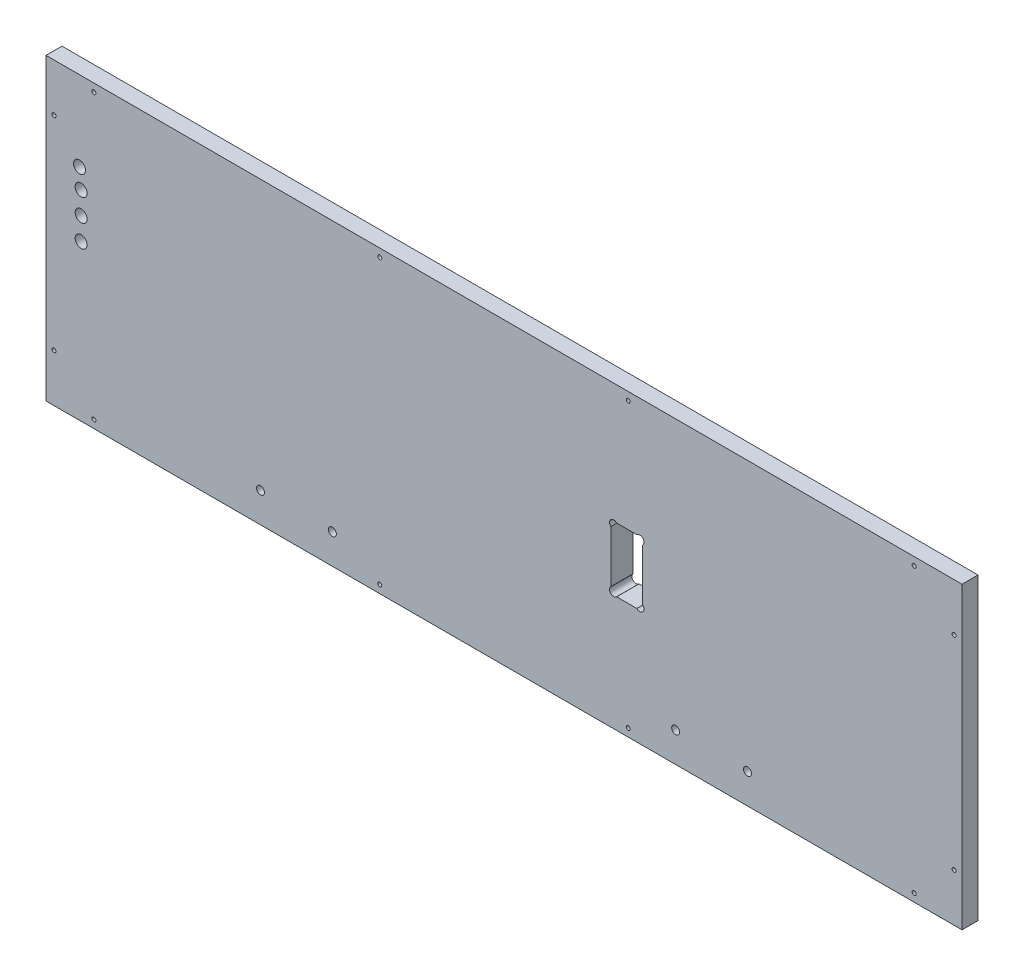
SolidWorks part; units mm, degrees
material "Pine"
ref_plane "Front Plane" through (0, 0, 0) normal (0, 0, 1) x (1, 0, 0)
ref_plane "Top Plane" through (0, 0, 0) normal (0, 1, 0) x (1, 0, 0)
ref_plane "Right Plane" through (0, 0, 0) normal (1, 0, 0) x (0, 0, -1)
sketch "Sketch1" plane through (0, 0, 0) normal (0, 0, 1) x (1, 0, 0)
  line L0 (-5300.6625, 1520.825) -> (-5451.475, 1520.825)
  line L1 (-5456.2375, 1384.3) -> (-5456.2375, 1516.0625)
  line L2 (-5557.8375, 1546.225) -> (-5194.3, 1546.225)
  line L3 (-5557.8375, 1539.875) -> (-5194.3, 1539.875)
  line L4 (-5297.4875, 1377.95) -> (-5454.65, 1377.95)
  line L5 (-5291.1375, 1384.3) -> (-5291.1375, 1516.0625)
  line L6 (-5300.6625, 1525.5875) -> (-5451.475, 1525.5875)
  line L7 (-5461, 1384.3) -> (-5461, 1516.0625)
  line L8 (-5297.4875, 1382.7125) -> (-5454.65, 1382.7125)
  line L9 (-5295.9, 1384.3) -> (-5295.9, 1516.0625)
  line L10 (-5740.4, 998.5375) -> (-5740.4, 1181.1)
  line L11 (-5740.4, 1181.1) -> (-5512.5938, 1181.1)
  line L12 (-5512.5938, 1181.1) -> (-5512.5938, 998.5375)
  line L13 (-5512.5938, 998.5375) -> (-5740.4, 998.5375)
  line L14 (-5258.5938, 1181.1) -> (-5486.4, 1181.1)
  line L15 (-5258.5938, 998.5375) -> (-5258.5938, 1181.1)
  line L16 (-5486.4, 998.5375) -> (-5258.5938, 998.5375)
  line L17 (-5486.4, 1181.1) -> (-5486.4, 998.5375)
  line L18 (-5740.4, 898.525) -> (-5011.7375, 898.525)
  line L19 (-5168.1062, 1384.3) -> (-5168.1062, 1392.2375)
  line L20 (-5176.0437, 1400.175) -> (-5245.8937, 1400.175)
  line L21 (-5253.8313, 1392.2375) -> (-5253.8313, 1384.3)
  line L22 (-5451.475, 1512.8875) -> (-5451.475, 1384.3)
  line L23 (-5303.8375, 1516.0625) -> (-5448.3, 1516.0625)
  line L24 (-5498.3062, 1384.3) -> (-5451.475, 1384.3)
  line L25 (-5253.8313, 1384.3) -> (-5300.6625, 1384.3)
  line L26 (-5584.0312, 1384.3) -> (-5740.4, 1384.3)
  line L27 (-5564.1875, 1536.7) -> (-5740.4, 1536.7)
  line L28 (-5740.4, 1357.3125) -> (-5740.4, 1206.5)
  line L29 (-5011.7375, 1357.3125) -> (-5740.4, 1357.3125)
  line L30 (-5011.7375, 1206.5) -> (-5011.7375, 1357.3125)
  line L31 (-5740.4, 1206.5) -> (-5011.7375, 1206.5)
  line L32 (-4765.675, 1549.4) -> (-4978.4, 1549.4)
  line L33 (-4765.675, 1397) -> (-4765.675, 1549.4)
  line L34 (-4978.4, 1397) -> (-4765.675, 1397)
  line L35 (-4978.4, 1549.4) -> (-4978.4, 1397)
  line L36 (-4765.675, 1371.6) -> (-4978.4, 1371.6)
  line L37 (-4765.675, 1219.2) -> (-4765.675, 1371.6)
  line L38 (-4978.4, 1219.2) -> (-4765.675, 1219.2)
  line L39 (-4978.4, 1371.6) -> (-4978.4, 1219.2)
  line L40 (-5284.7875, 803.275) -> (-5272.0875, 803.275)
  line L41 (-5187.95, 1536.7) -> (-5011.7375, 1536.7)
  line L42 (-5300.6625, 1384.3) -> (-5300.6625, 1512.8875)
  line L43 (-5740.4, 1536.7) -> (-5740.4, 1384.3)
  line L44 (-5557.8375, 1536.7) -> (-5557.8375, 1549.4)
  line L45 (-5557.8375, 1549.4) -> (-5194.3, 1549.4)
  line L46 (-5194.3, 1549.4) -> (-5194.3, 1536.7)
  line L47 (-5011.7375, 1536.7) -> (-5011.7375, 1384.3)
  line L48 (-5011.7375, 1384.3) -> (-5168.1062, 1384.3)
  line L49 (-5498.3062, 1384.3) -> (-5498.3062, 1392.2375)
  line L50 (-5506.2437, 1400.175) -> (-5576.0938, 1400.175)
  line L51 (-5584.0312, 1392.2375) -> (-5584.0312, 1384.3)
  line L52 (-5740.4, 660.4) -> (-5740.4, 898.525)
  line L53 (-5011.7375, 898.525) -> (-5011.7375, 660.4)
  line L54 (-5011.7375, 660.4) -> (-5740.4, 660.4)
  line L55 (-5291.1375, 803.275) -> (-5291.1375, 752.475)
  line L56 (-5265.7375, 752.475) -> (-5265.7375, 803.275)
  line L57 (-5284.7875, 752.475) -> (-5272.0875, 752.475)
  arc A0 (-5451.475, 1520.825) -> (-5456.2375, 1516.0625) centre (-5451.475, 1516.0625) ccw
  arc A1 (-5461, 1384.3) -> (-5454.65, 1377.95) centre (-5454.65, 1384.3) ccw
  arc A2 (-5297.4875, 1377.95) -> (-5291.1375, 1384.3) centre (-5297.4875, 1384.3) ccw
  circle A3 centre (-5037.9312, 1233.4875) radius 1.5875
  circle A4 centre (-5037.9312, 1328.7375) radius 1.5875
  circle A5 centre (-5714.2063, 1233.4875) radius 1.5875
  circle A6 centre (-5714.2063, 1328.7375) radius 1.5875
  circle A7 centre (-5018.0875, 1333.5) radius 1.5875
  circle A8 centre (-5018.0875, 1231.9) radius 1.5875
  circle A9 centre (-5734.05, 1231.9) radius 1.5875
  circle A10 centre (-5734.05, 1333.5) radius 1.5875
  circle A11 centre (-5734.05, 1511.3) radius 1.5875
  circle A12 centre (-5734.05, 1409.7) radius 1.5875
  circle A13 centre (-5018.0875, 1511.3) radius 1.5875
  circle A14 centre (-5018.0875, 1409.7) radius 1.5875
  arc A15 (-5557.8375, 1546.225) -> (-5557.8375, 1539.875) centre (-5557.8375, 1543.05) ccw
  arc A16 (-5194.3, 1539.875) -> (-5194.3, 1546.225) centre (-5194.3, 1543.05) ccw
  arc A17 (-5291.1375, 1516.0625) -> (-5300.6625, 1525.5875) centre (-5300.6625, 1516.0625) ccw
  arc A18 (-5451.475, 1525.5875) -> (-5461, 1516.0625) centre (-5451.475, 1516.0625) ccw
  arc A19 (-5456.2375, 1384.3) -> (-5454.65, 1382.7125) centre (-5454.65, 1384.3) ccw
  arc A20 (-5297.4875, 1382.7125) -> (-5295.9, 1384.3) centre (-5297.4875, 1384.3) ccw
  arc A21 (-5295.9, 1516.0625) -> (-5300.6625, 1520.825) centre (-5300.6625, 1516.0625) ccw
  circle A22 centre (-5702.3, 892.175) radius 1.5875
  circle A23 centre (-5734.05, 860.425) radius 1.5875
  circle A24 centre (-5474.8906, 892.175) radius 1.5875
  circle A25 centre (-5277.2469, 892.175) radius 1.5875
  circle A26 centre (-5049.8375, 892.175) radius 1.5875
  circle A27 centre (-5018.0875, 860.425) radius 1.5875
  circle A28 centre (-5296.6938, 1174.75) radius 1.5875
  circle A29 centre (-5448.3, 1174.75) radius 1.5875
  circle A30 centre (-5264.9437, 1155.7) radius 1.5875
  circle A31 centre (-5264.9437, 1023.9375) radius 1.5875
  circle A32 centre (-5518.9438, 1155.7) radius 1.5875
  circle A33 centre (-5518.9438, 1023.9375) radius 1.5875
  circle A34 centre (-5702.3, 1004.8875) radius 1.5875
  circle A35 centre (-5550.6937, 1004.8875) radius 1.5875
  arc A36 (-5576.0938, 1400.175) -> (-5584.0312, 1392.2375) centre (-5576.0938, 1392.2375) ccw
  arc A37 (-5168.1062, 1392.2375) -> (-5176.0437, 1400.175) centre (-5176.0437, 1392.2375) ccw
  arc A38 (-5245.8937, 1400.175) -> (-5253.8313, 1392.2375) centre (-5245.8937, 1392.2375) ccw
  arc A39 (-5448.3, 1516.0625) -> (-5451.475, 1512.8875) centre (-5448.3, 1512.8875) ccw
  arc A40 (-5284.7875, 803.275) -> (-5291.1375, 803.275) centre (-5287.9625, 803.275) ccw
  circle A41 centre (-5679.2812, 1026.3187) radius 1.5875
  circle A42 centre (-5679.2812, 1153.3187) radius 1.5875
  circle A43 centre (-5571.3313, 1153.3187) radius 1.5875
  circle A44 centre (-5571.3313, 1026.3187) radius 1.5875
  circle A45 centre (-5317.3312, 1153.3187) radius 1.5875
  circle A46 centre (-5317.3312, 1026.3187) radius 1.5875
  circle A47 centre (-5425.2812, 1026.3187) radius 1.5875
  circle A48 centre (-5425.2812, 1153.3187) radius 1.5875
  arc A49 (-5194.3, 1536.7) -> (-5187.95, 1536.7) centre (-5191.125, 1536.7) ccw
  arc A50 (-5564.1875, 1536.7) -> (-5557.8375, 1536.7) centre (-5561.0125, 1536.7) ccw
  arc A51 (-5300.6625, 1512.8875) -> (-5303.8375, 1516.0625) centre (-5303.8375, 1512.8875) ccw
  arc A52 (-5498.3062, 1392.2375) -> (-5506.2437, 1400.175) centre (-5506.2437, 1392.2375) ccw
  circle A53 centre (-5712.46, 784.225) radius 4.7625
  arc A54 (-5272.0875, 752.475) -> (-5265.7375, 752.475) centre (-5268.9125, 752.475) ccw
  arc A55 (-5291.1375, 752.475) -> (-5284.7875, 752.475) centre (-5287.9625, 752.475) ccw
  circle A56 centre (-5182.3938, 684.2125) radius 3.175
  circle A57 centre (-5239.5437, 684.2125) radius 3.175
  circle A58 centre (-5512.5938, 684.2125) radius 3.175
  circle A59 centre (-5569.7437, 684.2125) radius 3.175
  circle A60 centre (-5474.8906, 666.75) radius 1.5875
  circle A61 centre (-5277.2469, 666.75) radius 1.5875
  circle A62 centre (-5734.05, 698.5) radius 1.5875
  circle A63 centre (-5702.3, 666.75) radius 1.5875
  circle A64 centre (-5049.8375, 666.75) radius 1.5875
  circle A65 centre (-5018.0875, 698.5) radius 1.5875
  circle A66 centre (-5713.73, 835.025) radius 4.7625
  circle A67 centre (-5712.46, 819.785) radius 4.7625
  circle A68 centre (-5712.46, 802.005) radius 4.7625
  circle A69 centre (-5714.2063, 1314.45) radius 3.175
  circle A70 centre (-5037.9312, 1314.45) radius 3.175
  arc A71 (-5265.7375, 803.275) -> (-5272.0875, 803.275) centre (-5268.9125, 803.275) ccw
  ellipse E0 centre (-5371.3062, 1089.8188) end of major axis (-5277.6438, 1089.8188) minor radius 65.0875
  ellipse E1 centre (-5625.3062, 1089.8188) end of major axis (-5531.6438, 1089.8188) minor radius 65.0875
sketch "BackOutline" plane through (0, 0, 0) normal (0, 0, 1) x (1, 0, 0)
  line L0 (-5011.7375, 660.4) -> (-5011.7375, 898.525)
  line L1 (-5011.7375, 898.525) -> (-5740.4, 898.525)
  line L2 (-5740.4, 898.525) -> (-5740.4, 660.4)
  line L3 (-5740.4, 660.4) -> (-5011.7375, 660.4)
  line L4 (-5376.0688, 660.4) -> (-5376.0688, 898.525) construction
  line L5 (-5011.7375, 779.4625) -> (-5376.0688, 779.4625) construction
  line L6 (-5376.0688, 779.4625) -> (-5740.4, 779.4625) construction
  dimension "Length" = 728.6625
  dimension "Height" = 238.125
extrude "BackOutline_Thickness" add sketch "BackOutline" against normal blind 17.78
sketch "BcakHoles" plane through (0, 0, 0) normal (0, 0, 1) x (1, 0, 0)
  line L0 (-5291.1375, 803.275) -> (-5291.1375, 752.475)
  line L1 (-5265.7375, 803.275) -> (-5265.7375, 752.475)
  line L2 (-5291.1375, 803.275) -> (-5265.7375, 803.275)
  line L3 (-5291.1375, 752.475) -> (-5265.7375, 752.475)
  circle A0 centre (-5702.3, 892.175) radius 1.5875
  circle A1 centre (-5734.05, 860.425) radius 1.5875
  circle A6 centre (-5734.05, 698.5) radius 1.5875
  circle A7 centre (-5702.3, 666.75) radius 1.5875
  circle A8 centre (-5569.7437, 684.2125) radius 3.175
  circle A9 centre (-5512.5938, 684.2125) radius 3.175
  circle A10 centre (-5474.8906, 666.75) radius 1.5875
  circle A11 centre (-5277.2469, 666.75) radius 1.5875
  circle A12 centre (-5239.5437, 684.2125) radius 3.175
  circle A13 centre (-5182.3938, 684.2125) radius 3.175
  circle A14 centre (-5049.8375, 666.75) radius 1.5875
  circle A15 centre (-5018.0875, 698.5) radius 1.5875
  circle A16 centre (-5018.0875, 860.425) radius 1.5875
  circle A17 centre (-5049.8375, 892.175) radius 1.5875
  circle A18 centre (-5277.2469, 892.175) radius 1.5875
  circle A19 centre (-5474.8906, 892.175) radius 1.5875
extrude "Cut-Extrude1" cut sketch "BcakHoles" against normal up to surface (17.78 mm away) up to face at (-5376.0688, 779.4625, -17.78)
sketch "Sketch6" plane through (0, 0, 0) normal (0, 0, 1) x (1, 0, 0)
  line L0 (-5291.1375, 803.275) -> (-5288.8026, 800.9401) construction
  line L1 (-5265.7375, 803.275) -> (-5268.0724, 800.9401) construction
  line L2 (-5291.1375, 752.475) -> (-5288.8026, 754.8099) construction
  line L3 (-5265.7375, 752.475) -> (-5268.0724, 754.8099) construction
  circle A0 centre (-5288.8026, 800.9401) radius 3.302
  circle A1 centre (-5268.0724, 800.9401) radius 3.302
  circle A2 centre (-5288.8026, 754.8099) radius 3.302
  circle A3 centre (-5268.0724, 754.8099) radius 3.302
extrude "Cut-Extrude4" cut sketch "Sketch6" against normal up to surface (17.78 mm away) up to face at (-5278.4375, 777.875, -17.78)
sketch "BackPowerBoxLip" plane through (0, 660.4, 0) normal (0, -1, 0) x (1, 0, 0)
  line L0 (-5291.1375, -17.78) -> (-5291.1375, -8.255)
  line L3 (-5291.1375, -8.255) -> (-5461, -8.255)
  line L4 (-5461, -8.255) -> (-5461, -17.78)
  line L6 (-5461, -17.78) -> (-5291.1375, -17.78)
  line L7 (-5376.0688, -17.78) -> (-5376.0688, -8.255) construction
  line L8 (-5461, -13.0175) -> (-5376.0688, -13.0175) construction
  line L9 (-5291.1375, -13.0175) -> (-5376.0688, -13.0175) construction
  dimension "D1" = 169.8625
  dimension "D2" = 9.525
extrude "Cut-Extrude2" cut sketch "BackPowerBoxLip" against normal blind 3.175
sketch "BackLedge" plane through (0, 0, -17.78) normal (0, 0, -1) x (-1, 0, 0)
  line L0 (5011.7375, 660.4) -> (5113.3375, 660.4)
  line L1 (5291.1375, 660.4) -> (5011.7375, 660.4) construction
  line L2 (5113.3375, 660.4) -> (5113.3375, 673.1)
  line L3 (5113.3375, 673.1) -> (5024.4375, 673.1)
  line L4 (5024.4375, 673.1) -> (5024.4375, 885.825)
  line L5 (5024.4375, 885.825) -> (5727.7, 885.825)
  line L6 (5727.7, 885.825) -> (5727.7, 673.1)
  line L7 (5727.7, 673.1) -> (5638.8, 673.1)
  line L8 (5638.8, 673.1) -> (5638.8, 660.4)
  line L9 (5740.4, 660.4) -> (5461, 660.4) construction
  line L10 (5638.8, 660.4) -> (5740.4, 660.4)
  line L11 (5740.4, 660.4) -> (5740.4, 898.525)
  line L12 (5740.4, 898.525) -> (5011.7375, 898.525)
  line L13 (5011.7375, 898.525) -> (5011.7375, 660.4)
  dimension "D1" = 101.6
  dimension "D2" = 12.7
  dimension "D3" = 12.7
  dimension "D4" = 12.7
  dimension "D5" = 12.7
  dimension "D6" = 101.6
  dimension "D7" = 12.7
extrude "Cut-Extrude3" cut sketch "BackLedge" against normal blind 5.08
sketch "Sketch7" plane through (0, 0, -17.78) normal (0, 0, -1) x (-1, 0, 0)
  line L0 (5113.3375, 673.1) -> (5110.6125, 671.2352) construction
  line L1 (5638.8, 673.1) -> (5641.525, 671.2352) construction
  circle A0 centre (5641.525, 671.2352) radius 3.302
  circle A1 centre (5110.6125, 671.2352) radius 3.302
extrude "Cut-Extrude5" cut sketch "Sketch7" against normal up to surface (5.08 mm away) up to face at (-5735.6375, 860.425, -12.7)
sketch "BackAmpAccessHoles" plane through (0, 0, -17.78) normal (0, 0, -1) x (-1, 0, 0)
  line L0 (5727.7, 885.825) -> (5727.7, 673.1) construction
  circle A0 centre (5713.73, 835.025) radius 4.7625
  circle A1 centre (5712.46, 819.785) radius 4.7625
  circle A2 centre (5712.46, 802.005) radius 4.7625
  circle A3 centre (5712.46, 784.225) radius 4.7625
  dimension "D2" = 15.24
  dimension "D1" = 15.24
  dimension "D3" = 15.24
  dimension "D4" = 13.97
extrude "Cut-Extrude6" cut sketch "BackAmpAccessHoles" against normal up to surface (17.78 mm away) up to face at (-5278.4375, 777.875, 0)
